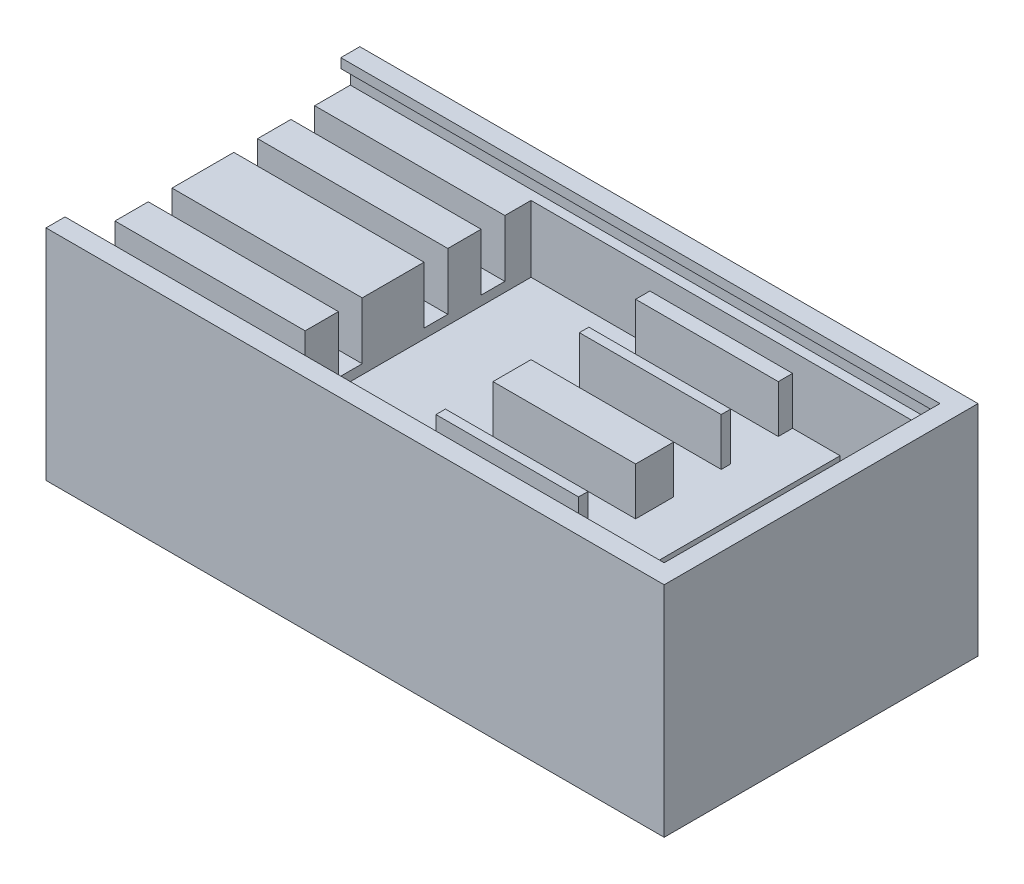
SolidWorks part; units mm, degrees
ref_plane "Front Plane" through (0, 0, 0) normal (0, 0, 1) x (1, 0, 0)
ref_plane "Top Plane" through (0, 0, 0) normal (0, 1, 0) x (1, 0, 0)
ref_plane "Right Plane" through (0, 0, 0) normal (1, 0, 0) x (0, 0, -1)
sketch "Sketch1" plane through (0, 0, 0) normal (0, 1, 0) x (1, 0, 0)
  line L1 (-32.5, -16.5) -> (32.5, -16.5)
  line L2 (-32.5, -16.5) -> (-32.5, 16.5)
  line L3 (-32.5, 16.5) -> (32.5, 16.5)
  line L4 (32.5, -16.5) -> (32.5, 16.5)
  line L5 (-32.5, -16.5) -> (32.5, 16.5) construction
  line L6 (-32.5, 16.5) -> (32.5, -16.5) construction
  point P0 (0, 0)
  dimension "D1" = 65
  dimension "D2" = 33
extrude "Boss-Extrude1" add sketch "Sketch1" along normal blind 2
sketch "Sketch2" plane through (0, 2, 0) normal (0, 1, 0) x (1, 0, 0)
  line L1 (-32.5, -16.5) -> (32.5, -16.5)
  line L2 (-32.5, -16.5) -> (-32.5, 16.5)
  line L3 (-32.5, 16.5) -> (32.5, 16.5)
  line L4 (32.5, -16.5) -> (32.5, 16.5)
  line L5 (-32.5, -16.5) -> (32.5, 16.5) construction
  line L6 (-32.5, 16.5) -> (32.5, -16.5) construction
  line L7 (30.5, -14.5) -> (-30.5, -14.5)
  line L8 (30.5, -14.5) -> (30.5, 14.5)
  line L9 (30.5, 14.5) -> (-30.5, 14.5)
  line L10 (-30.5, -14.5) -> (-30.5, 14.5)
  line L11 (30.5, -14.5) -> (-30.5, 14.5) construction
  line L12 (30.5, 14.5) -> (-30.5, -14.5) construction
  point P0 (0, 0)
  point P7 (0, 0)
  dimension "D1" = 2
  dimension "D2" = 2
extrude "Boss-Extrude2" add sketch "Sketch2" along normal blind 21
sketch "Sketch3" plane through (0, 2, 0) normal (0, 1, 0) x (1, 0, 0)
  line L0 (-30.5, -14.5) -> (30.5, -14.5) construction
  line L1 (-30.5, 14.5) -> (20, 14.5)
  line L2 (-30.5, 14.5) -> (-30.5, -14.5)
  line L3 (-30.5, -14.5) -> (20, -14.5)
  line L4 (20, 14.5) -> (20, -14.5)
  line L5 (30.5, -14.5) -> (30.5, 14.5) construction
  dimension "D1" = 10.5
extrude "Boss-Extrude3" add sketch "Sketch3" along normal blind 11
sketch "Sketch4" plane through (0, 2, 0) normal (0, 1, 0) x (1, 0, 0)
  line L0 (30.5, -14.5) -> (30.5, 14.5) construction
  line L1 (30.5, 14.5) -> (-30.5, 14.5) construction
  circle A0 centre (26.5, 0) radius 3
  point P4 (30.5, 0)
  dimension "D3" = 6
  dimension "D1" = 4
  dimension "D2" = 14.5
extrude "Cut-Extrude1" cut sketch "Sketch4" against normal blind 2
sketch "Sketch5" plane through (0, 2, 0) normal (0, 1, 0) x (1, 0, 0)
  line L1 (20, 14.5) -> (24, 14.5)
  line L2 (20, 14.5) -> (20, 8.5)
  line L3 (20, 8.5) -> (24, 8.5)
  line L4 (24, 14.5) -> (24, 8.5)
  dimension "D1" = 6
  dimension "D2" = 4
extrude "Boss-Extrude4" add sketch "Sketch5" along normal blind 9.5
sketch "Sketch6" plane through (0, 2, 0) normal (0, 1, 0) x (1, 0, 0)
  line L1 (20, -14.5) -> (24, -14.5)
  line L2 (20, -14.5) -> (20, -8.5)
  line L3 (20, -8.5) -> (24, -8.5)
  line L4 (24, -14.5) -> (24, -8.5)
  dimension "D1" = 4
  dimension "D2" = 6
extrude "Boss-Extrude5" add sketch "Sketch6" along normal blind 9.5
sketch "Sketch7" plane through (0, 2, 0) normal (0, 1, 0) x (1, 0, 0)
  line L0 (30.5, -14.5) -> (30.5, 14.5) construction
  line L1 (30.5, 4) -> (27.5, 4)
  line L2 (30.5, 4) -> (30.5, 8)
  line L3 (30.5, 8) -> (27.5, 8)
  line L4 (27.5, 4) -> (27.5, 8)
  line L5 (30.5, 14.5) -> (24, 14.5) construction
  point P8 (27.25, 14.5)
  dimension "D1" = 6.5
  dimension "D2" = 10.5
  dimension "D3" = 3
extrude "Boss-Extrude8" add sketch "Sketch7" along normal blind 9.5
sketch "Sketch9" plane through (0, 2, 0) normal (0, 1, 0) x (1, 0, 0)
  line L0 (30.5, -14.5) -> (30.5, 14.5) construction
  line L1 (30.5, -8) -> (27.5, -8)
  line L2 (30.5, -8) -> (30.5, -4)
  line L3 (30.5, -4) -> (27.5, -4)
  line L4 (27.5, -8) -> (27.5, -4)
  line L5 (24, -14.5) -> (30.5, -14.5) construction
  line L6 (-30.5, -14.5) -> (30.5, -14.5) construction
  dimension "D1" = 3
  dimension "D2" = 10.5
  dimension "D3" = 6.5
extrude "Boss-Extrude9" add sketch "Sketch9" along normal blind 9.5
sketch "Sketch10" plane through (0, 2, 0) normal (0, 1, 0) x (1, 0, 0)
  line L0 (20, -8.5) -> (20, 8.5) construction
  line L1 (20, -2) -> (23, -2)
  line L2 (20, -2) -> (20, 2)
  line L3 (20, 2) -> (23, 2)
  line L4 (23, -2) -> (23, 2)
  line L5 (30.5, 14.5) -> (24, 14.5) construction
  line L6 (20, -14.5) -> (24, -14.5) construction
  dimension "D1" = 3
  dimension "D2" = 12.5
  dimension "D3" = 12.5
extrude "Boss-Extrude10" add sketch "Sketch10" along normal blind 9.5
sketch "Sketch11" plane through (0, 23, 0) normal (0, 1, 0) x (1, 0, 0)
  line L0 (-32.5, 16.5) -> (-32.5, -16.5) construction
  line L1 (-30.5, 14.5) -> (-32.5, 14.5)
  line L2 (-30.5, 14.5) -> (-30.5, -14.5)
  line L3 (-30.5, -14.5) -> (-32.5, -14.5)
  line L4 (-32.5, 14.5) -> (-32.5, -14.5)
  line L5 (-32.5, -16.5) -> (32.5, -16.5) construction
  dimension "D1" = 2
extrude "Cut-Extrude2" cut sketch "Sketch11" against normal blind 3
sketch "Sketch13" plane through (-32.5, 0, 0) normal (-1, 0, 0) x (0, 0, 1)
  line L0 (-16.5, 23) -> (-16.5, 0) construction
  line L1 (-15.5, 20) -> (15.5, 20)
  line L2 (-15.5, 20) -> (-15.5, 22)
  line L3 (-15.5, 22) -> (15.5, 22)
  line L4 (15.5, 20) -> (15.5, 22)
  line L5 (16.5, 23) -> (16.5, 0) construction
  line L6 (14.5, 23) -> (-14.5, 23) construction
  point P4 (-15.5, 21)
  dimension "D1" = 1
  dimension "D2" = 1
  dimension "D3" = 3
  dimension "D4" = 1
extrude "Cut-Extrude3" cut sketch "Sketch13" against normal blind 63
sketch "Sketch14" plane through (0, 13, 0) normal (0, 1, 0) x (1, 0, 0)
  line L0 (20, 14.5) -> (-30.5, 14.5) construction
  line L1 (15, 14.5) -> (0, 14.5)
  line L2 (15, 14.5) -> (15, 13)
  line L3 (15, 13) -> (0, 13)
  line L4 (0, 14.5) -> (0, 13)
  line L5 (20, -14.5) -> (20, 14.5) construction
  dimension "D1" = 5
  dimension "D2" = 1.5
  dimension "D3" = 15
extrude "Boss-Extrude11" add sketch "Sketch14" along normal blind 5
sketch "Sketch15" plane through (0, 13, 0) normal (0, 1, 0) x (1, 0, 0)
  line L0 (-32.5, -14.5) -> (30.5, -14.5) construction
  line L1 (15, -14.5) -> (0, -14.5)
  line L2 (15, -14.5) -> (15, -13)
  line L3 (15, -13) -> (0, -13)
  line L4 (0, -14.5) -> (0, -13)
  line L5 (20, -14.5) -> (20, 14.5) construction
  point P8 (20, 0)
  dimension "D1" = 5
  dimension "D2" = 1.5
  dimension "D3" = 15
extrude "Boss-Extrude12" add sketch "Sketch15" along normal blind 5
sketch "Sketch16" plane through (0, 13, 0) normal (0, 1, 0) x (1, 0, 0)
  line L0 (20, -14.5) -> (20, 14.5) construction
  line L1 (15, 8) -> (0.0796, 8)
  line L2 (15, 8) -> (15, 7)
  line L3 (15, 7) -> (0.0796, 7)
  line L4 (0.0796, 8) -> (0.0796, 7)
  line L5 (0, 13) -> (15, 13) construction
  point P4 (15, 7.5)
  dimension "D1" = 5
  dimension "D2" = 14.9204
  dimension "D3" = 5
  dimension "D4" = 1
extrude "Boss-Extrude13" add sketch "Sketch16" along normal blind 5
sketch "Sketch17" plane through (0, 13, 0) normal (0, 1, 0) x (1, 0, 0)
  line L0 (20, -14.5) -> (20, 14.5) construction
  line L1 (15, -7) -> (0, -7)
  line L2 (15, -7) -> (15, -8)
  line L3 (15, -8) -> (0, -8)
  line L4 (0, -7) -> (0, -8)
  line L5 (15, -13) -> (0, -13) construction
  dimension "D1" = 5
  dimension "D2" = 15
  dimension "D3" = 1
  dimension "D4" = 5
extrude "Boss-Extrude14" add sketch "Sketch17" along normal blind 5
sketch "Sketch18" plane through (0, 13, 0) normal (0, 1, 0) x (1, 0, 0)
  line L0 (20, 2) -> (20, -2) construction
  line L1 (0, 2) -> (15, 2)
  line L2 (0, 2) -> (0, -2)
  line L3 (0, -2) -> (15, -2)
  line L4 (15, 2) -> (15, -2)
  line L5 (0.0796, 7) -> (15, 7) construction
  line L6 (15, -7) -> (0, -7) construction
  dimension "D1" = 5
  dimension "D2" = 15
  dimension "D3" = 5
  dimension "D4" = 5
extrude "Boss-Extrude15" add sketch "Sketch18" along normal blind 5
sketch "Sketch19" plane through (0, 13, 0) normal (0, 1, 0) x (1, 0, 0)
  line L0 (-30.5, -14.5) -> (0, -14.5) construction
  line L1 (-30.5, 14.5) -> (-12.5, 14.5)
  line L2 (-30.5, 14.5) -> (-30.5, -14.5)
  line L3 (-30.5, -14.5) -> (-12.5, -14.5)
  line L4 (-12.5, 14.5) -> (-12.5, -14.5)
  dimension "D1" = 18
extrude "Boss-Extrude16" add sketch "Sketch19" along normal blind 7
sketch "Sketch20" plane through (0, 20, 0) normal (0, 1, 0) x (1, 0, 0)
  line L0 (-32.5, 15.5) -> (-32.5, -15.5) construction
  line L1 (-32.5, 11.75) -> (-12.5, 11.75)
  line L2 (-32.5, 11.75) -> (-32.5, 9.25)
  line L3 (-32.5, 9.25) -> (-12.5, 9.25)
  line L4 (-12.5, 11.75) -> (-12.5, 9.25)
  line L5 (-12.5, -14.5) -> (-12.5, 14.5) construction
  line L6 (30.5, 14.5) -> (-32.5, 14.5) construction
  dimension "D1" = 2.75
  dimension "D2" = 2.5
extrude "Cut-Extrude4" cut sketch "Sketch20" against normal blind 6
sketch "Sketch21" plane through (0, 20, 0) normal (0, 1, 0) x (1, 0, 0)
  line L0 (-32.5, 9.25) -> (-32.5, -15.5) construction
  line L1 (-32.5, -9.25) -> (-12.5, -9.25)
  line L2 (-32.5, -9.25) -> (-32.5, -11.75)
  line L3 (-32.5, -11.75) -> (-12.5, -11.75)
  line L4 (-12.5, -9.25) -> (-12.5, -11.75)
  line L5 (-12.5, -14.5) -> (-12.5, 9.25) construction
  line L6 (-32.5, -14.5) -> (30.5, -14.5) construction
  dimension "D1" = 2.75
  dimension "D2" = 2.5
extrude "Cut-Extrude5" cut sketch "Sketch21" against normal blind 6
sketch "Sketch22" plane through (0, 20, 0) normal (0, 1, 0) x (1, 0, 0)
  line L0 (-32.5, 9.25) -> (-32.5, -9.25) construction
  line L1 (-32.5, 5.75) -> (-12.5, 5.75)
  line L2 (-32.5, 5.75) -> (-32.5, 3.25)
  line L3 (-32.5, 3.25) -> (-12.5, 3.25)
  line L4 (-12.5, 5.75) -> (-12.5, 3.25)
  line L5 (-12.5, -14.5) -> (-12.5, 14.5) construction
  line L6 (-32.5, 9.25) -> (-12.5, 9.25) construction
  dimension "D1" = 3.5
  dimension "D2" = 2.5
extrude "Cut-Extrude6" cut sketch "Sketch22" against normal blind 6
sketch "Sketch23" plane through (0, 20, 0) normal (0, 1, 0) x (1, 0, 0)
  line L0 (-32.5, 3.25) -> (-32.5, -9.25) construction
  line L1 (-32.5, -3.25) -> (-12.5, -3.25)
  line L2 (-32.5, -3.25) -> (-32.5, -5.75)
  line L3 (-32.5, -5.75) -> (-12.5, -5.75)
  line L4 (-12.5, -3.25) -> (-12.5, -5.75)
  line L5 (-12.5, -9.25) -> (-12.5, 3.25) construction
  line L6 (-12.5, -9.25) -> (-32.5, -9.25) construction
  dimension "D1" = 3.5
  dimension "D2" = 2.5
extrude "Cut-Extrude7" cut sketch "Sketch23" against normal blind 6
